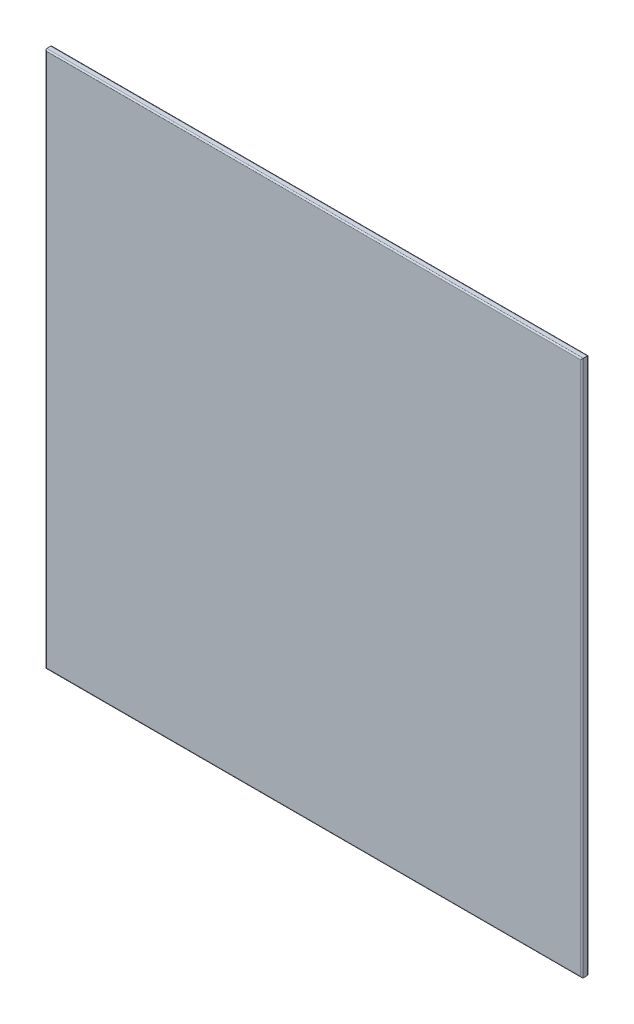
SolidWorks part; units mm, degrees
ref_plane "Front Plane" through (0, 0, 0) normal (0, 0, 1) x (1, 0, 0)
ref_plane "Top Plane" through (0, 0, 0) normal (0, 1, 0) x (1, 0, 0)
ref_plane "Right Plane" through (0, 0, 0) normal (1, 0, 0) x (0, 0, -1)
sketch "Sketch1" plane through (0, 0, 0) normal (0, 0, 1) x (1, 0, 0)
  line L1 (-610, -610) -> (610, -610)
  line L2 (-610, -610) -> (-610, 610)
  line L3 (-610, 610) -> (610, 610)
  line L4 (610, -610) -> (610, 610)
extrude "Boss-Extrude1" add sketch "Sketch1" along normal blind 15
fillet "Fillet1" radius 3 8 edges at (0, -610, 0) (610, 0, 0) (0, 610, 0) (-610, 0, 0) (0, 610, 15) (610, 0, 15) (0, -610, 15) (-610, 0, 15)
